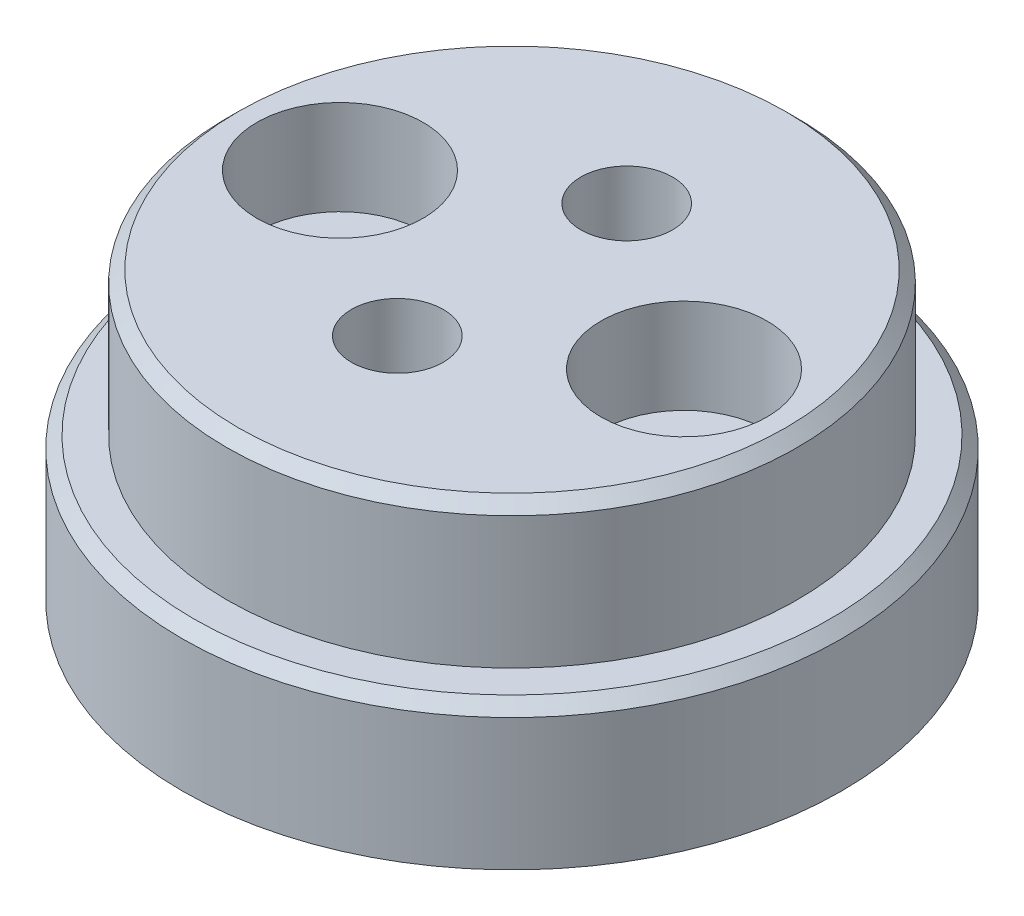
SolidWorks part; units mm, degrees
material "ABS"
ref_plane "Plan de face" through (0, 0, 0) normal (0, 0, 1) x (1, 0, 0)
ref_plane "Plan de dessus" through (0, 0, 0) normal (0, 1, 0) x (1, 0, 0)
ref_plane "Plan de droite" through (0, 0, 0) normal (1, 0, 0) x (0, 0, -1)
sketch "Esquisse1" plane through (0, 0, 0) normal (0, 1, 0) x (1, 0, 0)
  line L0 (0, 0) -> (0, 6) construction
  line L1 (-6, 0) -> (6, 0) construction
  circle A0 centre (0, 0) radius 11.5
  circle A1 centre (0, 0) radius 6 construction
  circle A2 centre (0, 6) radius 1.7 construction
  circle A3 centre (6, 0) radius 1.7
  circle A4 centre (0, -6) radius 1.7 construction
  circle A5 centre (-6, 0) radius 1.7
  circle A6 centre (0, 0) radius 4 construction
  circle A7 centre (0, 4) radius 1.6
  circle A8 centre (0, -4) radius 1.6
  circle A9 centre (0, 4) radius 2.25 construction
  point P15 (0, 0)
  dimension "D1" = 12
  dimension "D2" = 3.4
  dimension "D3" = 23
  dimension "D5" = 8
  dimension "D6" = 3.2
  dimension "D7" = 4.5
  dimension "D4" = 4
extrude "Boss.-Extru.1" add sketch "Esquisse1" along normal blind 5
sketch "Esquisse2" plane through (0, 5, 0) normal (0, 1, 0) x (1, 0, 0)
  circle A0 centre (0, 0) radius 9.95
  circle A2 centre (6, 0) radius 1.7 construction
  circle A3 centre (-6, 0) radius 1.7 construction
  circle A5 centre (0, -4) radius 1.6 construction
  circle A6 centre (6, 0) radius 1.7
  circle A7 centre (-6, 0) radius 1.7
  circle A8 centre (0, -4) radius 1.6
  circle A9 centre (0, 4) radius 1.6 construction
  circle A10 centre (0, 4) radius 1.6
  dimension "D1" = 19.9
extrude "Boss.-Extru.2" add sketch "Esquisse2" along normal blind 5
chamfer "Chanfrein2" distance 0.4 angle 45 1 edges at (0, 10, 9.95)
chamfer "Chanfrein4" distance 0.4 angle 45 1 edges at (0, 5, 11.5)
sketch "Esquisse3" plane through (0, 0, 0) normal (0, -1, 0) x (1, 0, 0)
  circle A0 centre (0, -4) radius 2.2
  circle A1 centre (0, 4) radius 2.2
  dimension "D1" = 4.4
  dimension "D2" = 4.4
extrude "Enlèv. mat.-Extru.1" cut sketch "Esquisse3" against normal blind 5.7
sketch "Esquisse4" plane through (0, 10, 0) normal (0, 1, 0) x (1, 0, 0)
  circle A0 centre (-6, 0) radius 2.9
  circle A1 centre (6, 0) radius 2.9
  dimension "D1" = 5.8
extrude "Enlèv. mat.-Extru.2" cut sketch "Esquisse4" against normal blind 3.3
